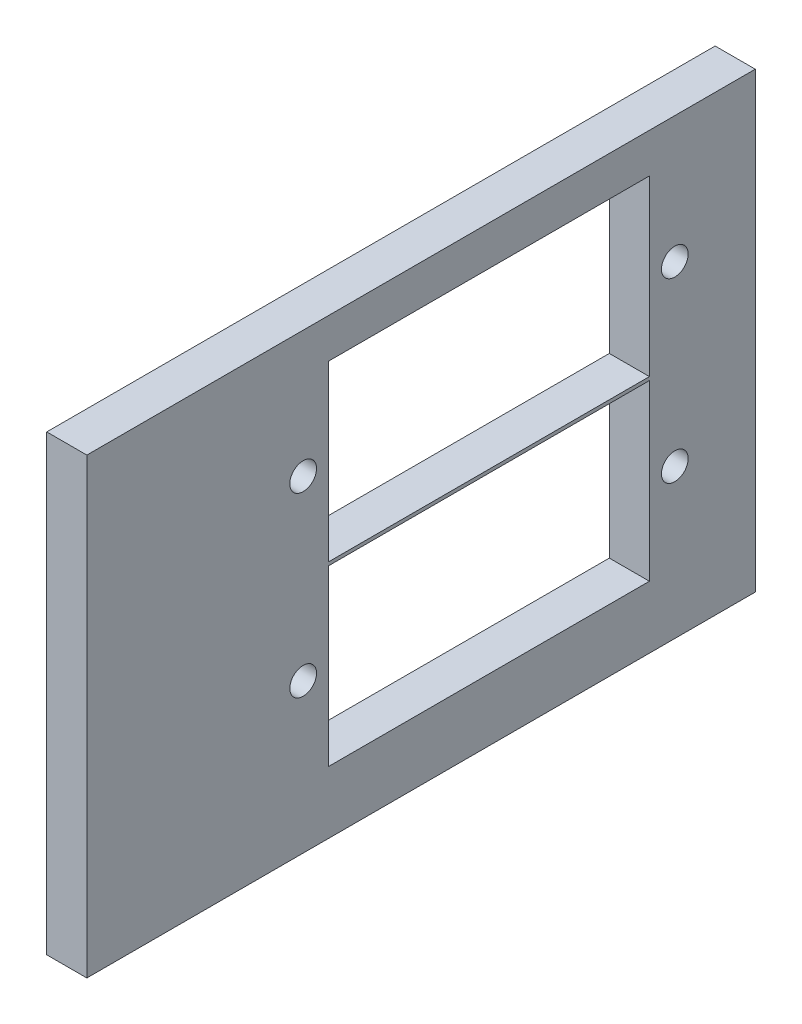
SolidWorks part; units mm, degrees
ref_plane "Front Plane" through (0, 0, 0) normal (0, 0, 1) x (1, 0, 0)
ref_plane "Top Plane" through (0, 0, 0) normal (0, 1, 0) x (1, 0, 0)
ref_plane "Right Plane" through (0, 0, 0) normal (1, 0, 0) x (0, 0, -1)
sketch "Sketch1" plane through (0, 0, 0) normal (1, 0, 0) x (0, 0, -1)
  line L1 (-8.9616, -56.7137) -> (41.0384, -56.7137)
  line L2 (-8.9616, -56.7137) -> (-8.9616, -22.8367)
  line L3 (-8.9616, -22.8367) -> (41.0384, -22.8367)
  line L4 (41.0384, -56.7137) -> (41.0384, -22.8367)
  point P0 (0, 0)
  point P6 (-26.677, -7.1003)
  point P7 (0, 0)
  point P9 (0, 0)
  point P11 (0, 0)
  point P13 (0, 0)
  point P14 (0, 0)
  point P15 (0, 0)
  point P17 (0, 0)
extrude "Boss-Extrude1" add sketch "Sketch1" along normal blind 3
sketch "Sketch2" plane through (0, 0, 0) normal (-1, 0, 0) x (0, 0, 1)
  line L0 (-21.1204, -39.0517) -> (-21.1204, -52.0517) construction
  line L1 (-33.1204, -39.0517) -> (-9.1204, -39.0517)
  line L2 (-33.1204, -39.0517) -> (-33.1204, -52.0517)
  line L3 (-33.1204, -52.0517) -> (-9.1204, -52.0517)
  line L4 (-9.1204, -39.0517) -> (-9.1204, -52.0517)
  line L5 (-33.1204, -39.0517) -> (-9.1204, -52.0517) construction
  line L6 (-33.1204, -52.0517) -> (-9.1204, -39.0517) construction
  line L7 (-21.1204, -25.794) -> (-21.1204, -38.794) construction
  line L8 (-33.1204, -25.794) -> (-9.1204, -25.794)
  line L9 (-33.1204, -25.794) -> (-33.1204, -38.794)
  line L10 (-33.1204, -38.794) -> (-9.1204, -38.794)
  line L11 (-9.1204, -25.794) -> (-9.1204, -38.794)
  line L12 (-33.1204, -25.794) -> (-9.1204, -38.794) construction
  line L13 (-33.1204, -38.794) -> (-9.1204, -25.794) construction
  circle A0 centre (-35.0204, -45.5517) radius 1
  circle A1 centre (-7.2204, -45.5517) radius 1
  circle A2 centre (-35.0204, -32.294) radius 1
  circle A3 centre (-7.2204, -32.294) radius 1
  point P9 (-21.1204, -45.5517)
  point P11 (-21.1204, -45.5517)
  point P21 (-21.1204, -32.294)
  point P23 (-21.1204, -32.294)
  dimension "D1" = 2
  dimension "D5" = 2
  dimension "D2" = 27.8
  dimension "D3" = 24
  dimension "D4" = 13
  dimension "D6" = 27.8
  dimension "D7" = 24
  dimension "D8" = 13
extrude "Cut-Extrude1" cut sketch "Sketch2" against normal through all
